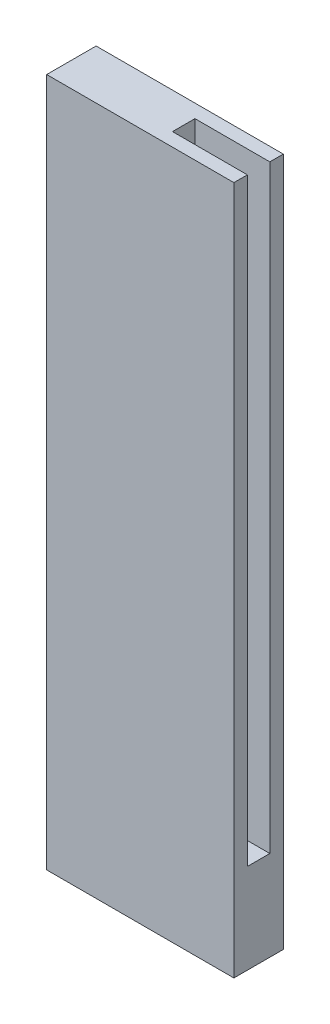
SolidWorks part; units mm, degrees
material "Mahogany"
ref_plane "Front Plane" through (0, 0, 0) normal (0, 0, 1) x (1, 0, 0)
ref_plane "Top Plane" through (0, 0, 0) normal (0, 1, 0) x (1, 0, 0)
ref_plane "Right Plane" through (0, 0, 0) normal (1, 0, 0) x (0, 0, -1)
sketch "Sketch1" plane through (0, 0, 0) normal (0, 0, 1) x (1, 0, 0)
  line L1 (0, 0) -> (-125, 0)
  line L2 (0, 0) -> (0, -460)
  line L3 (0, -460) -> (-125, -460)
  line L4 (-125, 0) -> (-125, -460)
  dimension "D1" = 125
  dimension "D2" = 460
extrude "Boss-Extrude1" add sketch "Sketch1" along normal blind 33
sketch "Sketch2" plane through (0, 0, 0) normal (0, 1, 0) x (1, 0, 0)
  line L0 (0, -33) -> (0, 0) construction
  line L1 (0, -9) -> (-50, -9)
  line L2 (0, -9) -> (0, -24)
  line L3 (0, -24) -> (-50, -24)
  line L4 (-50, -9) -> (-50, -24)
  line L5 (0, 0) -> (-125, 0) construction
  line L6 (0, -33) -> (-125, -33) construction
  dimension "D1" = 9
  dimension "D2" = 9
  dimension "D3" = 50
extrude "Cut-Extrude1" cut sketch "Sketch2" against normal blind 400
